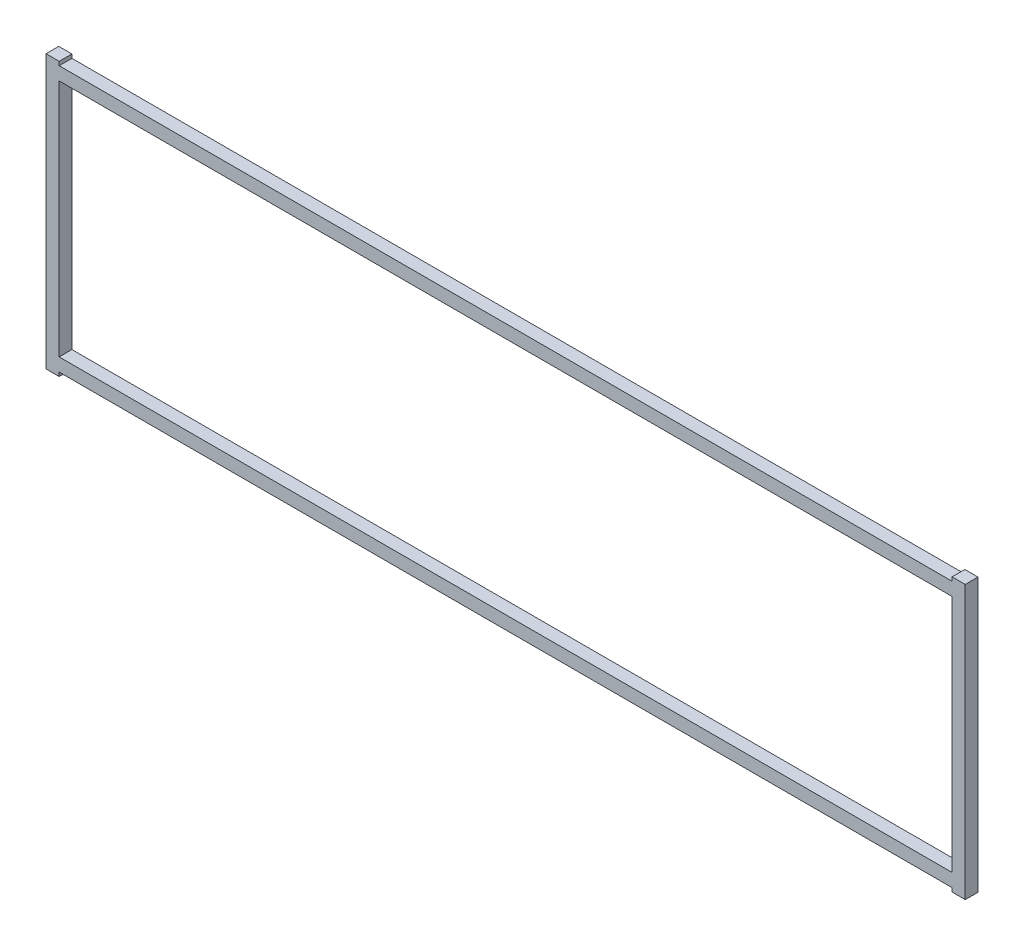
SolidWorks part; units mm, degrees
ref_plane "Front" through (0, 0, 0) normal (0, 0, 1) x (1, 0, 0)
ref_plane "Top" through (0, 0, 0) normal (0, 1, 0) x (1, 0, 0)
ref_plane "Right" through (0, 0, 0) normal (1, 0, 0) x (0, 0, -1)
sketch "Sketch1" plane through (0, 0, 0) normal (0, 0, 1) x (1, 0, 0)
  line L0 (222.1484, -67.9228) -> (228.7016, -67.9228)
  line L1 (228.7016, -67.9228) -> (228.7016, 67.9228)
  line L2 (228.7016, 67.9228) -> (222.1484, 67.9228)
  line L3 (222.1484, 67.9228) -> (222.1484, 66.0146)
  line L4 (222.1484, 66.0146) -> (-222.1484, 66.0146)
  line L5 (-222.1484, 66.0146) -> (-222.1484, 67.9228)
  line L6 (-222.1484, 67.9228) -> (-228.7016, 67.9228)
  line L7 (-228.7016, 67.9228) -> (-228.7016, -67.9228)
  line L8 (-228.7016, -67.9228) -> (-222.1484, -67.9228)
  line L9 (-222.1484, -67.9228) -> (-222.1484, -66.0146)
  line L10 (-222.1484, -66.0146) -> (222.1484, -66.0146)
  line L11 (222.1484, -66.0146) -> (222.1484, -67.9228)
  line L12 (222.1484, -59.4614) -> (222.1484, 59.4614)
  line L13 (-222.1484, -59.4614) -> (222.1484, -59.4614)
  line L14 (-222.1484, 59.4614) -> (-222.1484, -59.4614)
  line L15 (222.1484, 59.4614) -> (-222.1484, 59.4614)
extrude "Boss-Extrude1" add sketch "Sketch1" along normal blind 6.35
